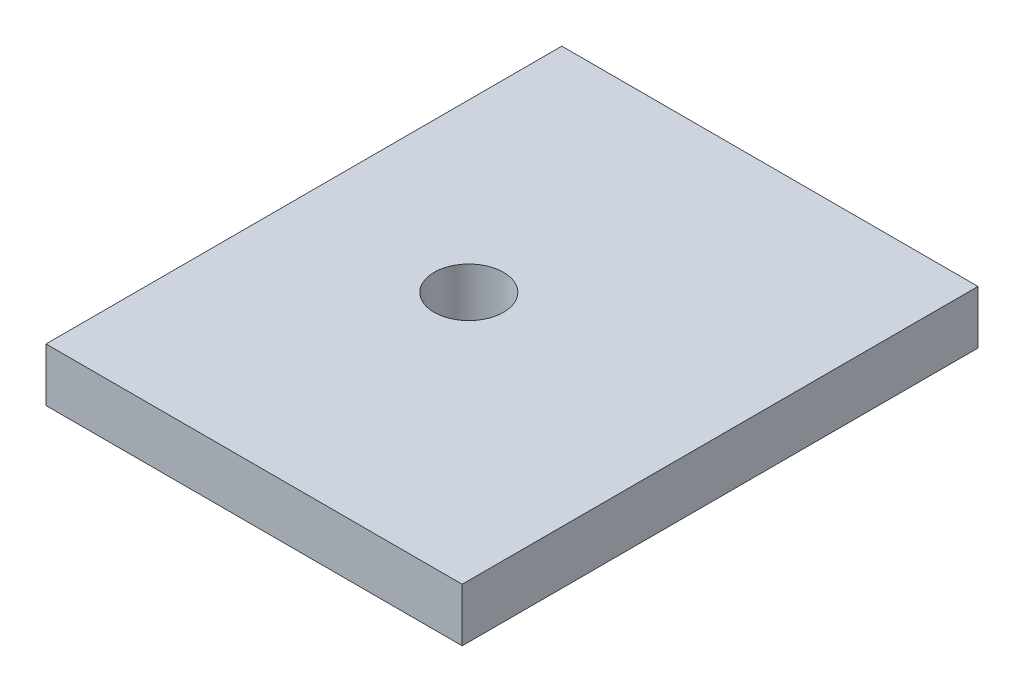
SolidWorks part; units mm, degrees
material "Custom Plastic"
ref_plane "Front Plane" through (0, 0, 0) normal (0, 0, 1) x (1, 0, 0)
ref_plane "Top Plane" through (0, 0, 0) normal (0, 1, 0) x (1, 0, 0)
ref_plane "Right Plane" through (0, 0, 0) normal (1, 0, 0) x (0, 0, -1)
sketch "Sketch1" plane through (0, 0, 0) normal (0, 1, 0) x (1, 0, 0)
  line L0 (-30.4611, 0) -> (33.997, 0) construction
  line L1 (-11.7, -14.5) -> (11.7, -14.5)
  line L2 (-11.7, -14.5) -> (-11.7, 14.5)
  line L3 (-11.7, 14.5) -> (11.7, 14.5)
  line L4 (11.7, -14.5) -> (11.7, 14.5)
  line L5 (-11.7, -14.5) -> (11.7, 14.5) construction
  line L6 (-11.7, 14.5) -> (11.7, -14.5) construction
  circle A0 centre (9, 8.9) radius 1
  circle A2 centre (9, -8.5) radius 1
  circle A3 centre (-9, -8.5) radius 1
  circle A5 centre (1.7, -8.5) radius 1
  spline S1 degree 3 poles (19.181, -14.2425) (19.8008, -12.3411) (17.8993, -11.7212) (17.2795, -13.6227) (16.6596, -15.5241) (18.5612, -16.144) (19.181, -14.2425) (19.8008, -12.3411) (17.8993, -11.7212) knots -0.5 0 0 0 0.5 0.5 0.5 1 1 1 1.5 1.5 1.5 weights 1 0.333333 0.333333 1 0.333333 0.333333 1 0.333333 0.333333 only from (19.181, -14.2425) to (19.181, -14.2425) construction
  spline S2 degree 3 poles (22.4885, -4.0962) (23.1083, -2.1947) (21.2068, -1.5749) (20.587, -3.4763) (19.9671, -5.3778) (21.8687, -5.9977) (22.4885, -4.0962) (23.1083, -2.1947) (21.2068, -1.5749) knots -0.5 0 0 0 0.5 0.5 0.5 1 1 1 1.5 1.5 1.5 weights 1 0.333333 0.333333 1 0.333333 0.333333 1 0.333333 0.333333 only from (22.4885, -4.0962) to (22.4885, -4.0962) construction
  spline S3 degree 3 poles (19.181, -14.2425) (19.8008, -12.3411) (17.8993, -11.7212) (17.2795, -13.6227) (16.6596, -15.5241) (18.5612, -16.144) (19.181, -14.2425) (19.8008, -12.3411) (17.8993, -11.7212) knots -0.5 0 0 0 0.5 0.5 0.5 1 1 1 1.5 1.5 1.5 weights 1 0.333333 0.333333 1 0.333333 0.333333 1 0.333333 0.333333 only from (19.181, -14.2425) to (19.181, -14.2425)
  spline S4 degree 3 poles (22.4885, -4.0962) (23.1083, -2.1947) (21.2068, -1.5749) (20.587, -3.4763) (19.9671, -5.3778) (21.8687, -5.9977) (22.4885, -4.0962) (23.1083, -2.1947) (21.2068, -1.5749) knots -0.5 0 0 0 0.5 0.5 0.5 1 1 1 1.5 1.5 1.5 weights 1 0.333333 0.333333 1 0.333333 0.333333 1 0.333333 0.333333 only from (22.4885, -4.0962) to (22.4885, -4.0962)
  point P0 (0, 0)
  point P6 (-9, 8.5)
  point P7 (9, 8.5)
  point P8 (9, 8.9)
  point P18 (1.7, 8.5)
  dimension "D7" = 17.4
  dimension "D8" = 18
  dimension "D10" = 2
  dimension "D1" = 29
  dimension "D2" = 23.4
  dimension "D3" = 6
  dimension "D4" = 6
  dimension "D5" = 18
  dimension "D6" = 2.7
  dimension "D9" = 10.7
extrude "Boss-Extrude1" add sketch "Sketch1" along normal blind 3
fillet "Fillet1" radius 2 4 edges at (11.7, 1.5, -14.5) (11.7, 1.5, 14.5) (-11.7, 1.5, 14.5) (-11.7, 1.5, -14.5)
sketch "Sketch5" plane through (0, 0, 0) normal (0, -1, 0) x (1, 0, 0)
  circle A0 centre (-2.1456, 3.6104) radius 2.5 construction
  circle A1 centre (-2.1456, 3.6104) radius 2.5 construction
  circle A2 centre (-2.1456, 3.6104) radius 1.44
  dimension "D1" = 2.88
extrude "Cut-Extrude3" cut sketch "Sketch5" against normal blind 10
sketch "Sketch7" plane through (0, 3, 0) normal (0, 1, 0) x (1, 0, 0)
  spline S0 degree 3 poles (19.181, -14.2425) (19.8008, -12.3411) (17.8993, -11.7212) (17.2795, -13.6227) (16.6596, -15.5241) (18.5612, -16.144) (19.181, -14.2425) (19.8008, -12.3411) (17.8993, -11.7212) knots -0.5 0 0 0 0.5 0.5 0.5 1 1 1 1.5 1.5 1.5 weights 1 0.333333 0.333333 1 0.333333 0.333333 1 0.333333 0.333333 only from (19.181, -14.2425) to (19.181, -14.2425) construction
  spline S1 degree 3 poles (22.4885, -4.0962) (23.1083, -2.1947) (21.2068, -1.5749) (20.587, -3.4763) (19.9671, -5.3778) (21.8687, -5.9977) (22.4885, -4.0962) (23.1083, -2.1947) (21.2068, -1.5749) knots -0.5 0 0 0 0.5 0.5 0.5 1 1 1 1.5 1.5 1.5 weights 1 0.333333 0.333333 1 0.333333 0.333333 1 0.333333 0.333333 only from (22.4885, -4.0962) to (22.4885, -4.0962) construction
  spline S2 degree 3 poles (19.181, -14.2425) (19.8008, -12.3411) (17.8993, -11.7212) (17.2795, -13.6227) (16.6596, -15.5241) (18.5612, -16.144) (19.181, -14.2425) (19.8008, -12.3411) (17.8993, -11.7212) knots -0.5 0 0 0 0.5 0.5 0.5 1 1 1 1.5 1.5 1.5 weights 1 0.333333 0.333333 1 0.333333 0.333333 1 0.333333 0.333333 only from (19.181, -14.2425) to (19.181, -14.2425)
  spline S3 degree 3 poles (22.4885, -4.0962) (23.1083, -2.1947) (21.2068, -1.5749) (20.587, -3.4763) (19.9671, -5.3778) (21.8687, -5.9977) (22.4885, -4.0962) (23.1083, -2.1947) (21.2068, -1.5749) knots -0.5 0 0 0 0.5 0.5 0.5 1 1 1 1.5 1.5 1.5 weights 1 0.333333 0.333333 1 0.333333 0.333333 1 0.333333 0.333333 only from (22.4885, -4.0962) to (22.4885, -4.0962)
extrude "Cut-Extrude4" cut sketch "Sketch7" against normal blind 10
sketch "Sketch8" plane through (0, 3, 0) normal (0, 1, 0) x (1, 0, 0)
  line L0 (24.633, 0) -> (-21.7502, 0) construction
  line L1 (1.7, -8.5) -> (1.7, 20.7764) construction
  line L2 (-9, -8.5) -> (-9, 21.3011) construction
  line L3 (9, -8.5) -> (9, 8.9) construction
  line L4 (14.3582, 8.9) -> (-23.7207, 8.9) construction
  circle A0 centre (1.7, 8.9) radius 1
  circle A1 centre (-9, 8.9) radius 1
  point P15 (1.7, 8.9)
  point P16 (-9, 8.9)
  dimension "D1" = 2
  dimension "D2" = 2
extrude "Cut-Extrude5" cut sketch "Sketch8" against normal blind 10
sketch "Sketch9" plane through (0, 3, 0) normal (0, 1, 0) x (1, 0, 0)
  circle A0 centre (-2.1456, -3.6104) radius 3.027
extrude "Boss-Extrude3" add sketch "Sketch9" against normal up to surface (3 mm away) up to face at (-9, 0, -9.9)
sketch "Sketch10" plane through (0, 3, 0) normal (0, 1, 0) x (1, 0, 0)
  circle A1 centre (-2.3282, -0.1) radius 1.5 construction
  circle A2 centre (-2.3282, -0.1) radius 1.95
  circle A3 centre (-2.3282, -0.1) radius 4 construction
  dimension "D1" = 3.9
extrude "Cut-Extrude6" cut sketch "Sketch10" against normal blind 10
sketch "Sketch13" plane through (0, 3, 0) normal (0, 1, 0) x (1, 0, 0)
  line L0 (-9.7, -14.5) -> (9.7, -14.5) construction
  line L1 (11.7, 14.5) -> (-11.7, 14.5)
  line L2 (11.7, 14.5) -> (11.7, -14.5)
  line L3 (11.7, -14.5) -> (-11.7, -14.5)
  line L4 (-11.7, 14.5) -> (-11.7, -14.5)
  line L5 (11.7, 14.5) -> (-11.7, -14.5) construction
  line L6 (11.7, -14.5) -> (-11.7, 14.5) construction
  line L7 (-11.7, 12.5) -> (-11.7, -12.5) construction
  circle A0 centre (-2.3282, -0.1) radius 1.95 construction
  circle A1 centre (-2.3282, -0.1) radius 1.95
  point P0 (0, 0)
  dimension "D1" = 0
  dimension "D2" = 0
extrude "Boss-Extrude4" add sketch "Sketch13" against normal up to surface (3 mm away) up to face at (-2.3282, 0, -1.85)
